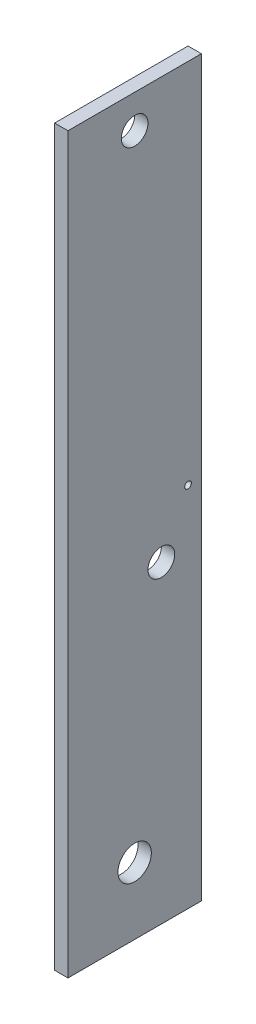
SolidWorks part; units mm, degrees
ref_plane "Front Plane" through (0, 0, 0) normal (0, 0, 1) x (1, 0, 0)
ref_plane "Top Plane" through (0, 0, 0) normal (0, 1, 0) x (1, 0, 0)
ref_plane "Right Plane" through (0, 0, 0) normal (1, 0, 0) x (0, 0, -1)
sketch "Sketch1" plane through (0, 0, 0) normal (1, 0, 0) x (0, 0, -1)
  line L1 (0, 0) -> (20, 0)
  line L2 (0, 0) -> (0, 110)
  line L3 (0, 110) -> (20, 110)
  line L4 (20, 0) -> (20, 110)
  dimension "D1" = 20
  dimension "D2" = 110
extrude "Boss-Extrude1" add sketch "Sketch1" along normal blind 2
sketch "Sketch2" plane through (2, 0, 0) normal (1, 0, 0) x (0, 0, -1)
  line L0 (20, 110) -> (0, 110) construction
  line L1 (20, 0) -> (20, 110) construction
  line L2 (0, 0) -> (20, 0) construction
  circle A0 centre (10, 10) radius 2.5
  circle A1 centre (10, 105) radius 2
  circle A2 centre (14, 47) radius 2
  circle A3 centre (18, 55) radius 0.5
  point P6 (10, 110)
  point P17 (17.6035, 0)
  dimension "D2" = 4
  dimension "D3" = 5
  dimension "D7" = 4
  dimension "D8" = 1
  dimension "D1" = 5
  dimension "D4" = 10
  dimension "D5" = 10
  dimension "D6" = 10
  dimension "D9" = 47
  dimension "D10" = 6
  dimension "D11" = 2
  dimension "D12" = 55
extrude "Cut-Extrude1" cut sketch "Sketch2" against normal blind 2
